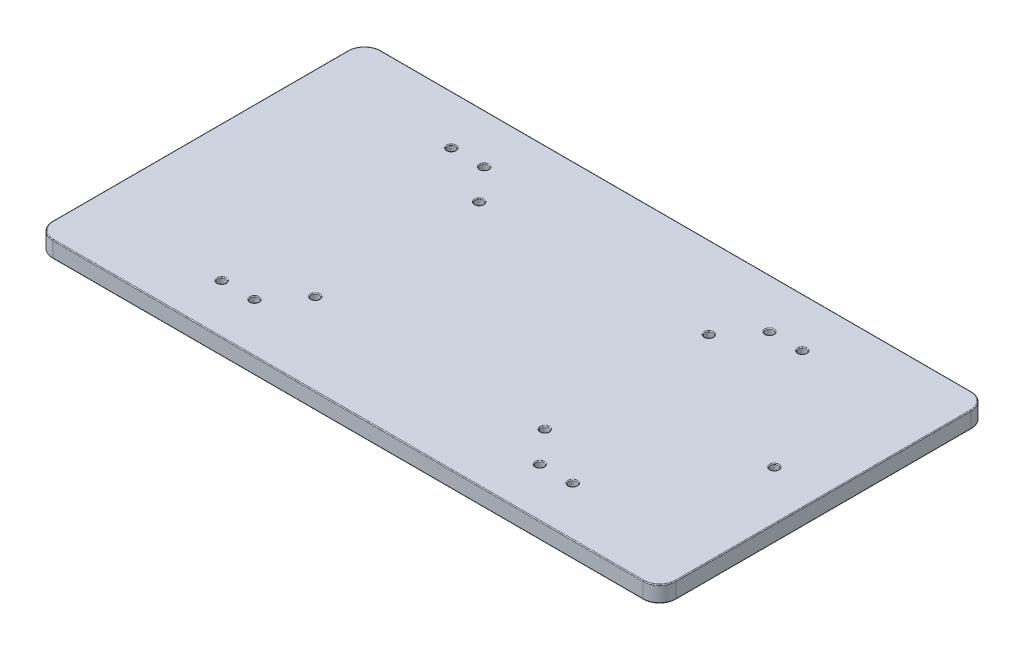
SolidWorks part; units mm, degrees
ref_plane "Front Plane" through (0, 0, 0) normal (0, 0, 1) x (1, 0, 0)
ref_plane "Top Plane" through (0, 0, 0) normal (0, 1, 0) x (1, 0, 0)
ref_plane "Right Plane" through (0, 0, 0) normal (1, 0, 0) x (0, 0, -1)
sketch "Sketch1" plane through (0, 0, 0) normal (0, 1, 0) x (1, 0, 0)
  line L0 (80, 50) -> (80, -50) construction
  line L1 (-95, 50) -> (95, 50)
  line L2 (-95, 50) -> (-95, -50)
  line L3 (-95, -50) -> (95, -50)
  line L4 (95, 50) -> (95, -50)
  line L5 (-95, 50) -> (95, -50) construction
  line L6 (-95, -50) -> (95, 50) construction
  line L7 (-35, 25) -> (35, 25) construction
  line L8 (-35, 25) -> (-35, -25) construction
  line L9 (-35, -25) -> (35, -25) construction
  line L10 (35, 25) -> (35, -25) construction
  line L11 (-35, 25) -> (35, -25) construction
  line L12 (-35, -25) -> (35, 25) construction
  line L13 (0, 0) -> (25.7133, 0) construction
  line L14 (0, 0) -> (0, 19.0047) construction
  circle A0 centre (-35, 25) radius 1.25
  circle A1 centre (35, 25) radius 1.25
  circle A2 centre (-35, -25) radius 1.25
  circle A3 centre (35, -25) radius 1.25
  circle A4 centre (80, 0) radius 1.25
  circle A5 centre (-53.5, -35) radius 1.25
  circle A6 centre (-43.5, -35) radius 1.25
  circle A7 centre (-43.5, 35) radius 1.25
  circle A8 centre (-53.5, 35) radius 1.25
  circle A9 centre (43.5, -35) radius 1.25
  circle A10 centre (53.5, -35) radius 1.25
  circle A11 centre (43.5, 35) radius 1.25
  circle A12 centre (53.5, 35) radius 1.25
  point P0 (0, 0)
  point P6 (0, 0)
  dimension "D5" = 2.5
  dimension "D7" = 2.5
  dimension "D8" = 2.5
  dimension "D9" = 10
  dimension "D1" = 190
  dimension "D2" = 100
  dimension "D3" = 70
  dimension "D4" = 50
  dimension "D6" = 15
  dimension "D10" = 43.5
  dimension "D11" = 15
extrude "Boss-Extrude1" add sketch "Sketch1" along normal blind 5
fillet "Fillet1" radius 5 4 edges at (95, 2.5, 50) (-95, 2.5, -50) (95, 2.5, -50) (-95, 2.5, 50)
fillet "Fillet2" radius 0.25 42 edges at (53.5, 0, -33.75) (53.5, 5, -33.75) (43.5, 0, -33.75) (43.5, 5, -33.75) (53.5, 0, 33.75) (53.5, 5, 33.75) (43.5, 0, 33.75) (43.5, 5, 33.75) (-53.5, 0, -36.25) (-53.5, 5, -36.25) (-43.5, 0, -36.25) (-43.5, 5, -36.25) (-43.5, 0, 36.25) (-43.5, 5, 36.25) (-53.5, 0, 36.25) (-53.5, 5, 36.25) (80, 0, 1.25) (80, 5, 1.25) (35, 0, 26.25) (35, 5, 26.25) (-35, 0, 26.25) (-35, 5, 26.25) (35, 0, -23.75) (35, 5, -23.75) (-35, 0, -23.75) (-35, 5, -23.75) (95, 0, 0) (0, 0, -50) (-95, 0, 0) (0, 0, 50) (95, 5, 0) (0, 5, -50) (-95, 5, 0) (-93.5355, 0, 48.5355) (93.5355, 0, -48.5355) (-93.5355, 0, -48.5355) (93.5355, 0, 48.5355) (-93.5355, 5, 48.5355) (93.5355, 5, -48.5355) (-93.5355, 5, -48.5355) (93.5355, 5, 48.5355) (0, 5, 50)
